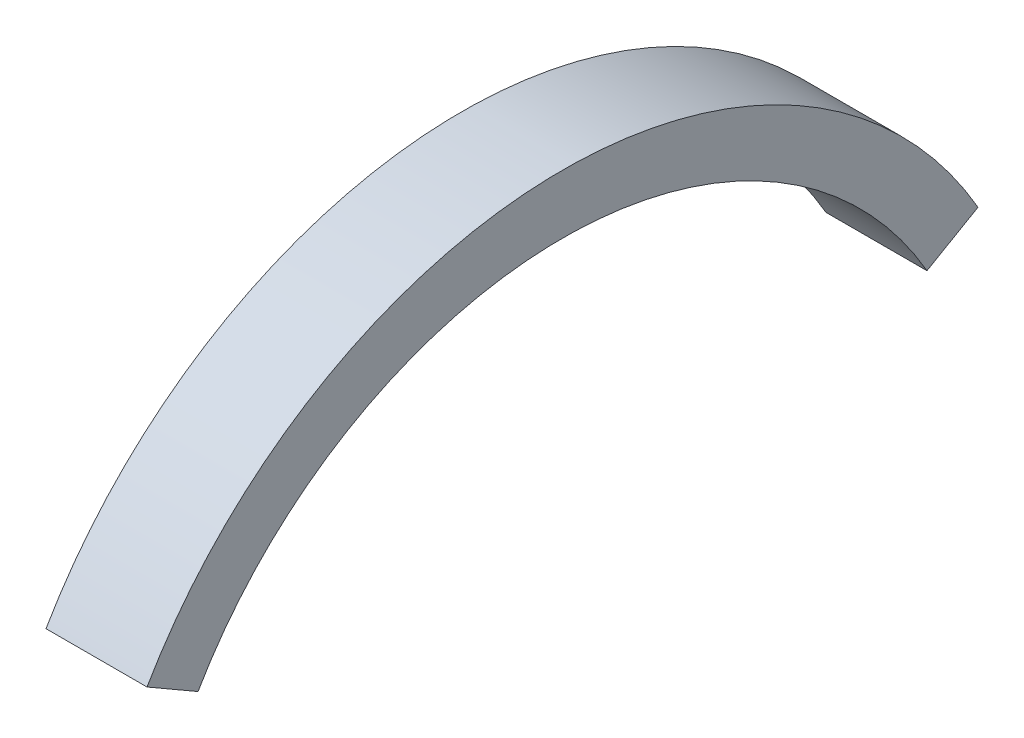
SolidWorks part; units mm, degrees
ref_plane "Front Plane" through (0, 0, 0) normal (0, 0, 1) x (1, 0, 0)
ref_plane "Top Plane" through (0, 0, 0) normal (0, 1, 0) x (1, 0, 0)
ref_plane "Right Plane" through (0, 0, 0) normal (1, 0, 0) x (0, 0, -1)
sketch "Sketch1" plane through (0, 0, 0) normal (1, 0, 0) x (0, 0, -1)
  line L0 (-37.3088, 0) -> (-28.5, 0) construction
  line L3 (28.5, 0) -> (40.5202, 0) construction
  line L4 (-24.6817, 14.25) -> (-21.6506, 12.5)
  line L5 (24.6817, 14.25) -> (21.6506, 12.5)
  arc A1 (24.6817, 14.25) -> (-24.6817, 14.25) centre (0, 0) ccw
  arc A2 (21.6506, 12.5) -> (-21.6506, 12.5) centre (0, 0) ccw
  dimension "D2" = 57
  dimension "D5" = 50
extrude "Boss-Extrude1" add sketch "Sketch1" along normal mid plane 6
